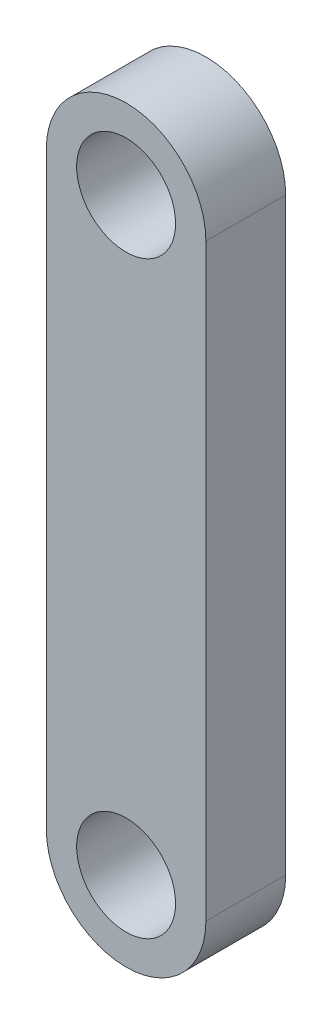
SolidWorks part; units mm, degrees
ref_plane "Front Plane" through (0, 0, 0) normal (0, 0, 1) x (1, 0, 0)
ref_plane "Top Plane" through (0, 0, 0) normal (0, 1, 0) x (1, 0, 0)
ref_plane "Right Plane" through (0, 0, 0) normal (1, 0, 0) x (0, 0, -1)
sketch "Sketch1" plane through (0, 0, 0) normal (0, 0, 1) x (1, 0, 0)
  line L0 (0, 33.503) -> (0, -13.36) construction
  line L1 (6.35, 33.503) -> (6.35, -13.36)
  line L2 (-6.35, 33.503) -> (-6.35, -13.36)
  arc A0 (6.35, 33.503) -> (-6.35, 33.503) centre (0, 33.503) ccw
  arc A1 (-6.35, -13.36) -> (6.35, -13.36) centre (0, -13.36) ccw
  circle A2 centre (0, 33.503) radius 3.937
  circle A3 centre (0, -13.36) radius 3.937
  point P3 (0, 10.0715)
  dimension "D1" = 7.874
  dimension "D2" = 7.874
  dimension "D3" = 46.863
  dimension "D4" = 12.7
extrude "Boss-Extrude1" add sketch "Sketch1" along normal blind 6.35
